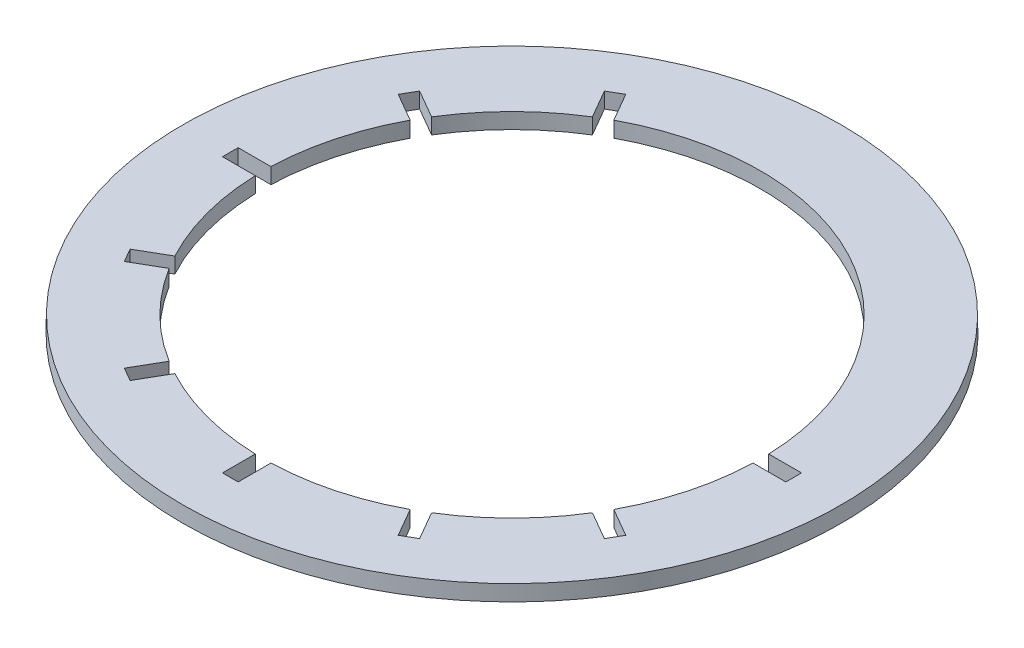
SolidWorks part; units mm, degrees
ref_plane "Front" through (0, 0, 0) normal (0, 0, 1) x (1, 0, 0)
ref_plane "Top" through (0, 0, 0) normal (0, 1, 0) x (1, 0, 0)
ref_plane "Right" through (0, 0, 0) normal (1, 0, 0) x (0, 0, -1)
sketch "Sketch1" plane through (0, 0, 0) normal (0, 1, 0) x (1, 0, 0)
  line L3 (-50.4239, 92.3368) -> (-54.754, 89.8368) construction
  circle A0 centre (0, 0) radius 79.4765
  circle A1 centre (0, 0) radius 105.1779
extrude "Boss-Extrude1" add sketch "Sketch1" along normal blind 5
sketch "Sketch2" plane through (0, 0, 0) normal (0, 0, 1) x (1, 0, 0)
  line L0 (105.1779, 0) -> (105.038, 6.3004)
  line L1 (105.038, 6.3004) -> (110.7433, 6.3004)
  line L2 (110.7433, 6.3004) -> (110.7433, 0)
  line L3 (110.7433, 0) -> (105.1779, 0)
  line L6 (0, 0) -> (0, 10.3268) construction
revolve "Cut-Revolve1" cut sketch "Sketch2" angle 360 about L6
sketch "Sketch3" plane through (0, 5, 0) normal (0, 1, 0) x (1, 0, 0)
  line L0 (0, 0) -> (114.5716, 0) construction
  line L1 (89.8949, -2.5) -> (64.0235, -2.5) construction
  line L2 (64.0235, -2.5) -> (89.8949, -2.5)
  line L3 (64.0235, -2.5) -> (64.0235, 2.5)
  line L4 (64.0235, 2.5) -> (89.8949, 2.5)
  line L5 (89.8949, -2.5) -> (89.8949, 2.5)
  line L6 (64.0235, -2.5) -> (89.8949, 2.5) construction
  line L7 (64.0235, 2.5) -> (89.8949, -2.5) construction
  line L8 (64.0235, -2.5) -> (64.0235, 2.5) construction
  point P2 (76.9592, 0)
  dimension "D1" = 5
extrude "Cut-Extrude1" cut sketch "Sketch3" against normal up to next (5 mm away)
pattern_circular "CirPattern1" count 9 every 30 about axis through (0, 0, 0) along (0, 1, 0) of "Cut-Extrude1"
